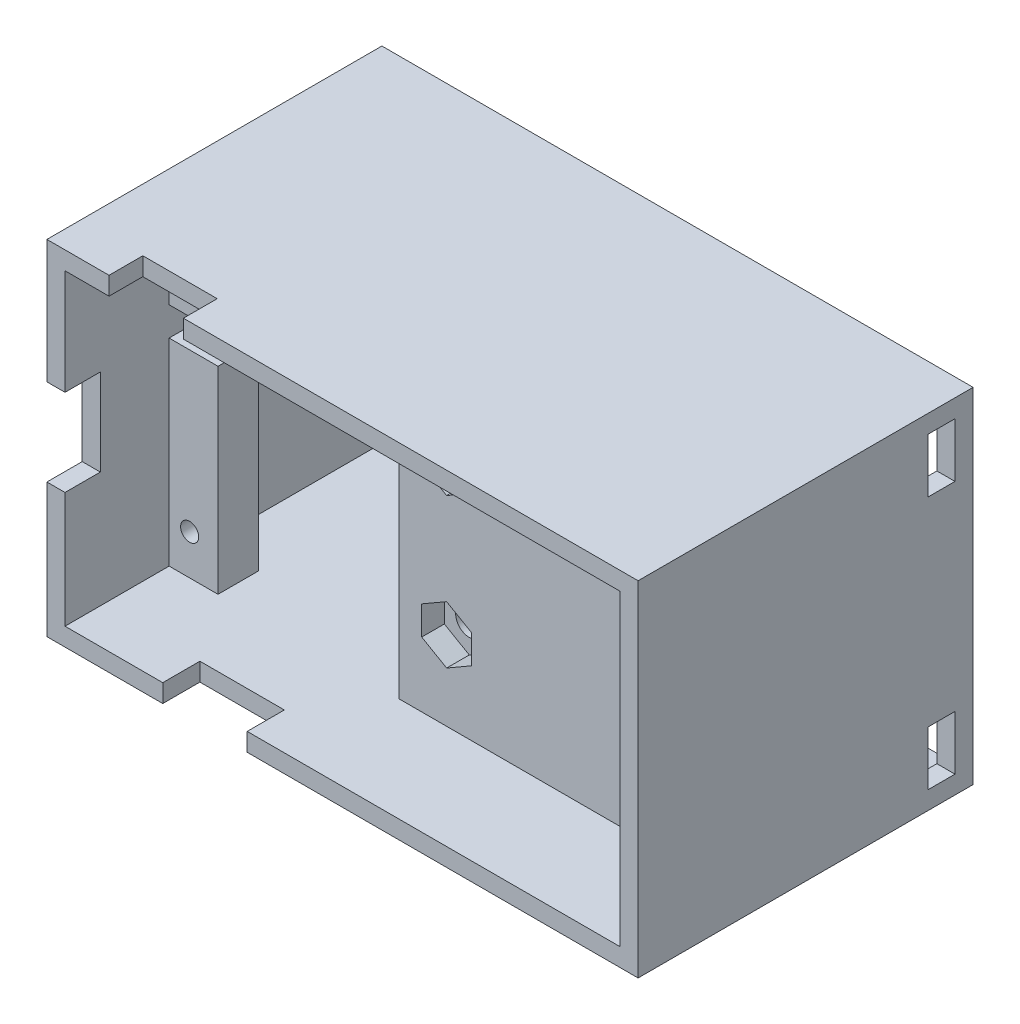
SolidWorks part; units mm, degrees
other "标注1"
sketch "草图16" plane through (3.3763, -43.0665, -26) normal (0.531, -0.7584, -0.3779) x (-0.8474, -0.4776, -0.2321)
other "标注2"
sketch "草图17" plane through (-61.9234, -43.0665, 5.5) normal (-0.5977, -0.3514, 0.7206) x (0.795, -0.3761, 0.4759)
ref_plane "前视基准面" through (0, 0, 0) normal (0, 0, 1) x (1, 0, 0)
ref_plane "上视基准面" through (0, 0, 0) normal (0, 1, 0) x (1, 0, 0)
ref_plane "右视基准面" through (0, 0, 0) normal (1, 0, 0) x (0, 0, -1)
ref_plane "基准面1" through (0, 0, 3.6001) normal (0, 0, 1) x (1, 0, 0)
sketch "草图1" plane through (0, 0, 3.6001) normal (0, 0, 1) x (1, 0, 0)
  line L0 (0.8763, -38.7224) -> (-59.4234, -38.7224) construction
  line L1 (-48.7034, -33.8618) -> (-39.801, -33.8618)
  line L2 (-48.7034, -33.8618) -> (-48.7034, -38.7224)
  line L4 (-39.801, -33.8618) -> (-39.801, -38.7224)
  line L5 (-59.4234, -9.4107) -> (0.8763, -9.4107) construction
  line L7 (-55.7687, -9.4107) -> (-55.7687, -14.2907)
  line L8 (-55.7687, -14.2907) -> (-45.8066, -14.2907)
  line L9 (-45.8066, -9.4107) -> (-45.8066, -14.2907)
  line L10 (-12.699, -17.609) -> (-12.699, -12.109) construction
  line L11 (0.8763, -9.4107) -> (-45.8066, -9.4107)
  line L12 (0.8763, -9.4107) -> (0.8763, -38.7224)
  line L13 (0.8763, -38.7224) -> (-39.801, -38.7224)
  line L14 (-59.4234, -9.4107) -> (-59.4234, -19.2521)
  line L15 (-29.2736, -33.0846) -> (-20.6538, -33.0846)
  line L16 (-29.2736, -33.0846) -> (-29.2736, -36.2921)
  line L17 (-29.2736, -36.2921) -> (-20.6538, -36.2921)
  line L18 (-20.6538, -33.0846) -> (-20.6538, -36.2921)
  line L23 (-12.699, -12.109) -> (-9.399, -12.109)
  line L24 (-12.699, -12.109) -> (-12.699, -17.609)
  line L25 (-12.699, -17.609) -> (-9.399, -17.609)
  line L26 (-9.399, -12.109) -> (-9.399, -17.609)
  line L27 (-48.7034, -38.7224) -> (-59.4234, -38.7224)
  line L28 (-55.7687, -9.4107) -> (-59.4234, -9.4107)
  line L29 (-59.4234, -27.6866) -> (-59.4234, -38.7224)
  line L30 (-59.4234, -19.2521) -> (-54.3557, -19.2521)
  line L32 (-59.4234, -27.6866) -> (-54.3557, -27.6866)
  line L33 (-54.3557, -19.2521) -> (-54.3557, -27.6866)
  circle A0 centre (-57.6581, -36.6498) radius 1
  circle A1 centre (-57.6581, -11.2498) radius 1
  circle A2 centre (-1.016, -11.2498) radius 1
  circle A3 centre (-0.889, -36.8301) radius 1
  circle A4 centre (-4.1259, -29.4689) radius 1.322
  circle A5 centre (-5.9082, -27.2775) radius 0.4462
  circle A6 centre (-4.5737, -26.6799) radius 0.4462
  circle A7 centre (-3.1192, -26.8297) radius 0.4462
  circle A8 centre (-1.9345, -27.6866) radius 0.4462
  circle A9 centre (-1.3369, -29.0211) radius 0.4462
  circle A10 centre (-1.4866, -30.4756) radius 0.4462
  circle A11 centre (-2.3435, -31.6603) radius 0.4462
  circle A12 centre (-3.678, -32.2579) radius 0.4462
  circle A13 centre (-5.1325, -32.1082) radius 0.4462
  circle A14 centre (-6.3173, -31.2513) radius 0.4462
  circle A15 centre (-6.9149, -29.9168) radius 0.4462
  circle A16 centre (-6.7652, -28.4623) radius 0.4462
  point P71 (-4.1259, -29.4689)
  dimension "D1" = 12
ref_plane "基准面2" through (0, 0, -6) normal (0, 0, -1) x (-1, 0, 0)
sketch "草图2" plane through (0, 0, -6) normal (0, 0, -1) x (-1, 0, 0)
  line L0 (29.2736, -9.4107) -> (29.2736, -38.7224) construction
  line L1 (-0.8763, -38.7224) -> (59.4234, -38.7224)
  line L2 (-0.8763, -38.7224) -> (-0.8763, -9.4107)
  line L3 (-0.8763, -9.4107) -> (59.4234, -9.4107)
  line L4 (59.4234, -38.7224) -> (59.4234, -9.4107)
  line L5 (59.4234, -24.0665) -> (-9.3078, -24.0665) construction
  line L6 (-3.3763, -5.0665) -> (61.9234, -43.0665) construction
  line L9 (29.2736, -15.8165) -> (29.2736, -13.1836) construction
  line L10 (27.7854, -15.8165) -> (27.7854, -13.1836)
  line L11 (30.7617, -15.8165) -> (30.7617, -13.1836)
  line L12 (29.2736, -38.7224) -> (29.2736, -43.3487) construction
  line L13 (-3.3763, -43.0665) -> (61.9234, -5.0665) construction
  line L14 (-3.3763, -5.0665) -> (61.9234, -5.0665)
  line L15 (-3.3763, -5.0665) -> (-3.3763, -43.0665)
  line L16 (-3.3763, -43.0665) -> (61.9234, -43.0665)
  line L17 (61.9234, -5.0665) -> (61.9234, -43.0665)
  circle A0 centre (1.016, -11.2498) radius 1
  circle A1 centre (0.889, -36.8301) radius 1
  circle A2 centre (57.6581, -36.6498) radius 1
  circle A3 centre (57.6581, -11.2498) radius 0.9222
  arc A10 (27.7854, -15.8165) -> (30.7617, -15.8165) centre (29.2736, -15.8165) ccw
  arc A11 (30.7617, -13.1836) -> (27.7854, -13.1836) centre (29.2736, -13.1836) ccw
  circle A12 centre (29.2736, -32.3165) radius 1.5
  point P24 (29.2736, -24.0665)
  point P27 (29.2736, -31.5665)
  point P28 (29.2736, -24.0665)
  point P33 (29.2736, -14.5001)
  dimension "D1" = 38
  dimension "D2" = 2.5
  dimension "D3" = 3
  dimension "D4" = 8.25
  dimension "D5" = 2.5
  dimension "D7" = 8.25
extrude "凸台-拉伸2" add sketch "草图2" along normal blind 4.5 separate body
sketch "草图3" plane through (0, 0, -6) normal (0, 0, -1) x (-1, 0, 0)
  line L0 (29.2736, -15.8165) -> (29.2736, -10.8487) construction
  line L1 (32.0236, -17.4043) -> (32.0236, -14.2288)
  line L4 (26.5236, -14.2288) -> (26.5236, -17.4043)
  line L5 (26.5236, -17.4043) -> (29.2736, -18.992)
  line L6 (29.2736, -18.992) -> (32.0236, -17.4043)
  line L8 (32.0236, -14.9203) -> (32.0236, -11.7449)
  line L9 (32.0236, -11.7449) -> (29.2736, -10.1572)
  line L10 (29.2736, -10.1572) -> (26.5236, -11.7449)
  line L11 (26.5236, -11.7449) -> (26.5236, -14.9203)
  line L14 (31.8974, -14.9932) -> (32.0236, -14.9203) [skipped]
  line L15 (29.2736, -22.4541) -> (17.663, -22.4541) construction
  line L16 (29.2736, -22.4541) -> (29.2736, -17.3047) construction
  line L17 (26.6497, -14.156) -> (26.5236, -14.2288) [skipped]
  line L18 (26.5236, -14.9203) -> (26.6497, -14.9932) [skipped]
  line L19 (32.0236, -14.2288) -> (31.8974, -14.156) [skipped]
  line L20 (26.5236, -33.9043) -> (29.2736, -35.492)
  line L21 (29.2736, -35.492) -> (32.0236, -33.9043)
  line L22 (32.0236, -33.9043) -> (32.0236, -30.7288)
  line L23 (32.0236, -30.7288) -> (29.2736, -29.1411)
  line L24 (29.2736, -29.1411) -> (26.5236, -30.7288)
  line L25 (26.5236, -30.7288) -> (26.5236, -33.9043)
  arc A0 (26.82, -14.5746) -> (31.7271, -14.5746) centre (29.2736, -15.8165) ccw construction
  arc A1 (31.7271, -14.5746) -> (26.82, -14.5746) centre (29.2736, -13.3326) ccw construction
  circle A2 centre (29.2736, -32.3165) radius 2.75 construction
  circle A3 centre (1.016, -11.2498) radius 1.75
  circle A4 centre (57.6581, -11.2498) radius 1.75
  arc A5 (27.7854, -15.8165) -> (30.7617, -15.8165) centre (29.2736, -15.8165) ccw construction
  circle A6 centre (0.889, -36.8301) radius 1.75
  circle A7 centre (57.6581, -36.6498) radius 1.75
  point P25 (29.2736, -33.8241)
  dimension "D2" = 3.5
  dimension "D1" = 5.5
extrude "切除-拉伸2" cut sketch "草图3" along normal blind 2.5 contours L10 L11 L4 L5 L6 L1 L8 L9 | L24 L25 L20 L21 L22 L23
sketch "草图5" plane through (0, 0, -10.5) normal (0, 0, -1) x (-1, 0, 0)
  line L0 (29.2736, -7.0665) -> (29.2736, -48.0798) construction
  line L5 (-1.3763, -7.0665) -> (59.9234, -7.0665)
  line L6 (-1.3763, -7.0665) -> (-1.3763, -41.0665)
  line L7 (-1.3763, -41.0665) -> (59.9234, -41.0665)
  line L8 (59.9234, -7.0665) -> (59.9234, -41.0665)
  line L9 (-3.3763, -5.0665) -> (61.9234, -5.0665)
  line L10 (-3.3763, -5.0665) -> (-3.3763, -43.0665)
  line L11 (-3.3763, -43.0665) -> (61.9234, -43.0665)
  line L12 (61.9234, -5.0665) -> (61.9234, -43.0665)
  line L13 (-0.8763, -9.4107) -> (59.4234, -38.7224) construction
  line L14 (-1.3763, -7.0665) -> (59.9234, -41.0665) construction
  line L15 (-3.3763, -5.0665) -> (61.9234, -43.0665) construction
  line L16 (61.9234, -5.0665) -> (-3.3763, -43.0665) construction
  point P12 (29.2736, -24.0665)
  point P13 (29.2736, -24.0665)
  point P18 (29.2736, -24.0665)
  dimension "D1" = 61.2997
  dimension "D2" = 38
  dimension "D3" = 34
  dimension "D4" = 2
extrude "凸台-拉伸3" add sketch "草图5" along normal blind 21 and the other way blind 16
sketch "草图7" plane through (0, -5.0665, 0) normal (0, 1, 0) x (1, 0, 0)
  line L0 (-41.7981, -5.5601) -> (-46.8481, -5.5601) construction
  line L1 (-55.0622, -1.765) -> (-46.8481, -1.765)
  line L2 (-55.0622, -1.765) -> (-55.0622, -5.5601)
  line L3 (-55.0622, -5.5601) -> (-46.8481, -5.5601)
  line L4 (-46.8481, -1.765) -> (-46.8481, -5.5601)
extrude "切除-拉伸4" cut sketch "草图7" against normal blind 3
sketch "草图8" plane through (-61.9234, 0, 0) normal (-1, 0, 0) x (0, 0, 1)
  line L0 (5.6001, -27.6866) -> (5.6001, -38.7224) construction
  line L1 (1.6001, -18.6953) -> (5.6001, -18.6953)
  line L2 (1.6001, -18.6953) -> (1.6001, -28.2708)
  line L3 (1.6001, -28.2708) -> (5.6001, -28.2708)
  line L4 (5.6001, -18.6953) -> (5.6001, -28.2708)
  dimension "D1" = 4
extrude "切除-拉伸5" cut sketch "草图8" against normal blind 3
sketch "草图9" plane through (0, -43.0665, 0) normal (0, -1, 0) x (1, 0, 0)
  line L0 (-59.4234, 5.6001) -> (-48.7034, 5.6001) construction
  line L1 (-49.1273, 5.6001) -> (-39.801, 5.6001)
  line L2 (-49.1273, 5.6001) -> (-49.1273, 1.3978)
  line L3 (-49.1273, 1.3978) -> (-39.801, 1.3978)
  line L4 (-39.801, 5.6001) -> (-39.801, 1.3978)
extrude "切除-拉伸6" cut sketch "草图9" against normal blind 3
sketch "草图13" plane through (0, 0, -6) normal (0, 0, 1) x (1, 0, 0)
  line L2 (-59.9234, -16.0665) -> (-59.9234, -19.2521)
  line L3 (-59.9234, -19.2521) -> (-54.5253, -19.2521)
  line L5 (-59.9234, -16.0665) -> (-54.5253, -16.0665)
  line L6 (-49.1273, -41.0665) -> (-59.9234, -41.0665) construction
  line L7 (-54.5253, -41.0665) -> (-34.5253, -41.0665)
  line L8 (-54.5253, -41.0665) -> (-54.5253, -19.2521)
  line L9 (-54.5253, -7.0665) -> (-34.5253, -7.0665)
  line L10 (-34.5253, -41.0665) -> (-34.5253, -7.0665)
  line L11 (-46.8481, -7.0665) -> (1.3763, -7.0665) construction
  line L12 (-54.5253, -16.0665) -> (-54.5253, -12.8809)
  line L13 (-54.5253, -12.8809) -> (-54.5253, -7.0665)
  dimension "D2" = 20
extrude "切除-拉伸7" cut sketch "草图13" against normal blind 10
sketch "草图15" plane through (0, 0, -10.5) normal (0, 0, -1) x (-1, 0, 0)
  circle A0 centre (1.016, -11.2498) radius 1.75
  circle A1 centre (57.6581, -11.2498) radius 1.75
  circle A2 centre (0.889, -36.8301) radius 1.75
  circle A3 centre (57.6581, -36.6498) radius 1.75
  dimension "D1" = 3.5
extrude "切除-拉伸8" cut sketch "草图15" against normal blind 1.5
sketch "草图18" plane through (0, 0, -31.5) normal (0, 0, -1) x (-1, 0, 0)
  line L0 (59.9234, -7.0665) -> (-1.3763, -7.0665) construction
  line L1 (-1.3763, -6.0665) -> (60.9234, -6.0665)
  line L2 (-1.3763, -6.0665) -> (-1.3763, -42.0665)
  line L3 (-1.3763, -42.0665) -> (60.9234, -42.0665)
  line L4 (60.9234, -6.0665) -> (60.9234, -42.0665)
  line L5 (-1.3763, -41.0665) -> (34.5253, -41.0665) construction
  line L6 (61.9234, -43.0665) -> (61.9234, -5.0665) construction
  dimension "D1" = 1
  dimension "D2" = 1
  dimension "D3" = 1
extrude "切除-拉伸9" cut sketch "草图18" against normal blind 3
sketch "草图19" plane through (1.3763, 0, 0) normal (-1, 0, 0) x (0, 0, 1)
  line L0 (-31.5, -43.0665) -> (-31.5, -5.0665) construction
  line L1 (-29.5, -7.0665) -> (-26.5, -7.0665)
  line L2 (-29.5, -7.0665) -> (-29.5, -13.0665)
  line L3 (-29.5, -13.0665) -> (-26.5, -13.0665)
  line L4 (-26.5, -7.0665) -> (-26.5, -13.0665)
  line L5 (-31.5, -5.0665) -> (5.5, -5.0665) construction
  line L6 (-31.5, -24.0665) -> (15.6063, -24.0665) construction
  line L7 (-29.5, -35.0665) -> (-26.5, -35.0665)
  line L8 (-26.5, -41.0665) -> (-26.5, -35.0665)
  line L9 (-29.5, -41.0665) -> (-26.5, -41.0665)
  line L10 (-29.5, -41.0665) -> (-29.5, -35.0665)
  dimension "D1" = 2
  dimension "D2" = 3
  dimension "D3" = 2
  dimension "D4" = 6
extrude "切除-拉伸10" cut sketch "草图19" against normal blind 2
sketch "草图20" plane through (0, 0, -31.5) normal (0, 0, -1) x (-1, 0, 0)
  line L0 (-1.3763, -24.0665) -> (97.3122, -24.0665) construction
  line L1 (-1.3763, -6.0665) -> (-1.3763, -42.0665) construction
  line L2 (59.9234, -42.0665) -> (59.9234, -6.0665) construction
  line L3 (59.9234, -20.0665) -> (61.9234, -20.0665)
  line L4 (59.9234, -20.0665) -> (59.9234, -28.0665)
  line L5 (59.9234, -28.0665) -> (61.9234, -28.0665)
  line L6 (61.9234, -20.0665) -> (61.9234, -28.0665)
  line L7 (61.9234, -43.0665) -> (61.9234, -5.0665) construction
  line L8 (59.9234, -20.0665) -> (61.9234, -28.0665) construction
  line L9 (61.9234, -20.0665) -> (59.9234, -28.0665) construction
  point P12 (60.9234, -24.0665)
  dimension "D1" = 8
extrude "切除-拉伸11" cut sketch "草图20" against normal blind 3
sketch "草图21" plane through (-61.9234, 0, 0) normal (-1, 0, 0) x (0, 0, 1)
  line L0 (-28.5, -28.0665) -> (-31.5, -28.0665) construction
  line L1 (-28.5, -20.0665) -> (-24, -20.0665)
  line L2 (-28.5, -20.0665) -> (-28.5, -28.0665)
  line L3 (-28.5, -28.0665) -> (-24, -28.0665)
  line L4 (-24, -20.0665) -> (-24, -28.0665)
  dimension "D1" = 4.5
extrude "凸台-拉伸4" add sketch "草图21" along normal blind 8
sketch "草图22" plane through (0, 0, -24) normal (0, 0, 1) x (1, 0, 0)
  line L0 (-61.9234, -24.0665) -> (-80.0935, -24.0665) construction
  line L1 (-61.9234, -28.0665) -> (-61.9234, -20.0665) construction
  line L2 (-61.9234, -18.6953) -> (-61.9234, -28.2708) construction
  circle A0 centre (-65.9234, -24.0665) radius 1.5
  dimension "D1" = 3
  dimension "D2" = 4
extrude "切除-拉伸12" cut sketch "草图22" against normal blind 10
sketch "草图23" plane through (0, 0, -24) normal (0, 0, 1) x (1, 0, 0)
  line L0 (-69.9234, -20.0665) -> (-61.9234, -20.0665) construction
  line L1 (-64.3357, -26.8165) -> (-62.748, -24.0665)
  line L2 (-62.748, -24.0665) -> (-64.3357, -21.3165)
  line L3 (-64.3357, -21.3165) -> (-67.5111, -21.3165)
  line L4 (-67.5111, -21.3165) -> (-69.0988, -24.0665)
  line L5 (-69.0988, -24.0665) -> (-67.5111, -26.8165)
  line L6 (-67.5111, -26.8165) -> (-64.3357, -26.8165)
  circle A0 centre (-65.9234, -24.0665) radius 2.75 construction
  dimension "D1" = 5.5
extrude "切除-拉伸13" cut sketch "草图23" against normal blind 2.5
fillet "圆角1" radius 1 2 edges at (-69.9234, -28.0665, -26.25) (-69.9234, -20.0665, -26.25)
